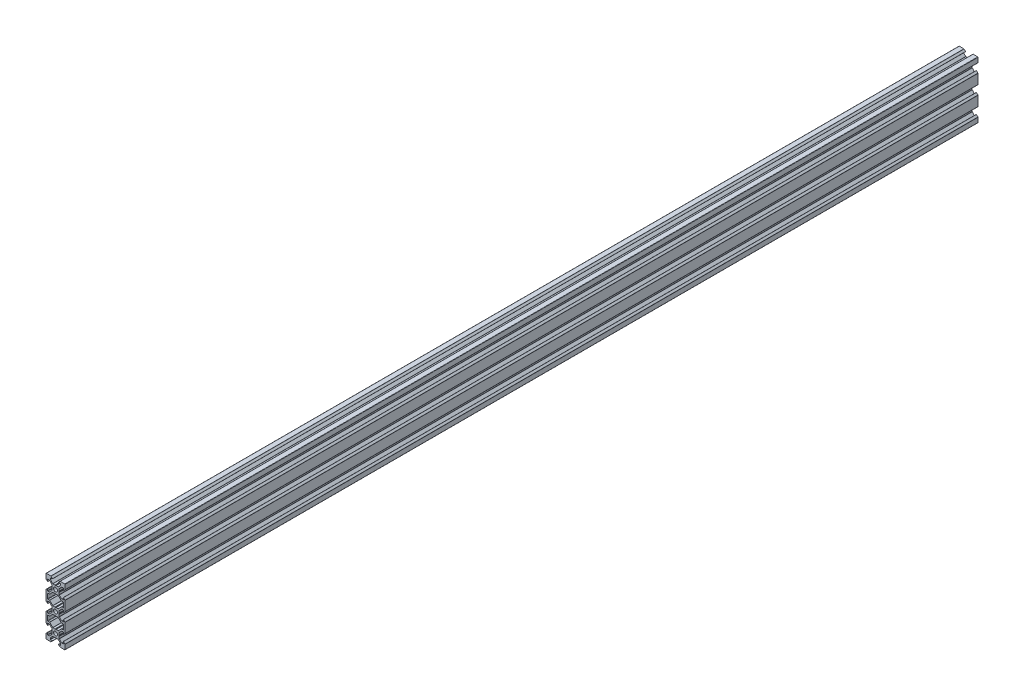
SolidWorks part; units mm, degrees
material "6063-T5"
ref_plane "Plan de face" through (0, 0, 0) normal (0, 0, 1) x (1, 0, 0)
ref_plane "Plan de dessus" through (0, 0, 0) normal (0, 1, 0) x (1, 0, 0)
ref_plane "Plan de droite" through (0, 0, 0) normal (1, 0, 0) x (0, 0, -1)
sketch "Esquisse1" plane through (0, 0, 0) normal (0, 0, 1) x (1, 0, 0)
  line L12 (10.4135, -7.6873) -> (8.8378, -7.6873)
  line L13 (8.6256, -7.5995) -> (5.4414, -4.4152)
  line L14 (5.2292, -4.3273) -> (3.0331, -4.3273)
  line L15 (3.0331, -4.3273) -> (2.5135, -4.0273)
  line L16 (2.5135, -4.0273) -> (1.9939, -4.3273)
  line L17 (1.9939, -4.3273) -> (-0.2022, -4.3273)
  line L18 (-0.4144, -4.4152) -> (-3.5986, -7.5995)
  line L19 (-3.8108, -7.6873) -> (-5.3865, -7.6873)
  line L20 (-5.6865, -7.9873) -> (-5.6865, -10.4267)
  line L21 (-5.6865, -10.4267) -> (-5.6865, -12.866)
  line L22 (-5.3865, -13.166) -> (-3.8108, -13.166)
  line L23 (-3.5986, -13.2539) -> (-0.4144, -16.4382)
  line L24 (-0.2022, -16.526) -> (1.9939, -16.526)
  line L25 (1.9939, -16.526) -> (2.5135, -16.826)
  line L26 (2.5135, -16.826) -> (3.0331, -16.526)
  line L27 (3.0331, -16.526) -> (5.2292, -16.526)
  line L28 (5.4414, -16.4382) -> (8.6256, -13.2539)
  line L29 (8.8378, -13.166) -> (10.4135, -13.166)
  line L30 (10.7135, -12.866) -> (10.7135, -10.4267)
  line L31 (10.7135, -10.4267) -> (10.7135, -7.9873)
  line L38 (10.4135, 12.3127) -> (8.8378, 12.3127)
  line L39 (8.6256, 12.4005) -> (5.4414, 15.5848)
  line L40 (5.2292, 15.6727) -> (3.0331, 15.6727)
  line L41 (3.0331, 15.6727) -> (2.5135, 15.9727)
  line L42 (2.5135, 15.9727) -> (1.9939, 15.6727)
  line L43 (1.9939, 15.6727) -> (-0.2022, 15.6727)
  line L44 (-0.4144, 15.5848) -> (-3.5986, 12.4005)
  line L45 (-3.8108, 12.3127) -> (-5.3865, 12.3127)
  line L46 (-5.6865, 12.0127) -> (-5.6865, 9.5733)
  line L47 (-5.6865, 9.5733) -> (-5.6865, 7.134)
  line L48 (-5.3865, 6.834) -> (-3.8108, 6.834)
  line L49 (-3.5986, 6.7461) -> (-0.4144, 3.5618)
  line L50 (-0.2022, 3.474) -> (1.9939, 3.474)
  line L51 (1.9939, 3.474) -> (2.5135, 3.174)
  line L52 (2.5135, 3.174) -> (3.0331, 3.474)
  line L53 (3.0331, 3.474) -> (5.2292, 3.474)
  line L54 (5.4414, 3.5618) -> (8.6256, 6.7461)
  line L55 (8.8378, 6.834) -> (10.4135, 6.834)
  line L56 (10.7135, 7.134) -> (10.7135, 9.5733)
  line L57 (10.7135, 9.5733) -> (10.7135, 12.0127)
  line L64 (6.1142, 19.5733) -> (6.4142, 20.0929)
  line L65 (6.4142, 20.0929) -> (6.4142, 22.2891)
  line L66 (6.502, 22.5012) -> (8.9856, 24.9848)
  line L67 (9.1978, 25.0727) -> (10.4135, 25.0727)
  line L68 (10.7135, 24.7727) -> (10.7135, 22.7733)
  line L69 (10.8842, 22.7026) -> (12.4256, 24.244)
  line L70 (12.5135, 24.4562) -> (12.5135, 29.2733)
  line L71 (12.2135, 29.5733) -> (7.3963, 29.5733)
  line L72 (7.1842, 29.4855) -> (5.6428, 27.944)
  line L73 (5.7135, 27.7733) -> (7.7128, 27.7733)
  line L74 (8.0128, 27.4733) -> (8.0128, 26.2576)
  line L75 (7.925, 26.0455) -> (5.4414, 23.5618)
  line L78 (5.2292, 23.474) -> (3.0331, 23.474)
  line L79 (3.0331, 23.474) -> (2.5135, 23.174)
  line L80 (2.5135, 23.174) -> (1.9939, 23.474)
  line L81 (1.9939, 23.474) -> (-0.2022, 23.474)
  line L84 (-0.4144, 23.5618) -> (-2.898, 26.0455)
  line L85 (-2.9858, 26.2576) -> (-2.9858, 27.4733)
  line L86 (-2.6858, 27.7733) -> (-0.6865, 27.7733)
  line L87 (-0.6158, 27.944) -> (-2.1572, 29.4855)
  line L88 (-2.3693, 29.5733) -> (-7.1865, 29.5733)
  line L89 (-7.4865, 29.2733) -> (-7.4865, 24.4562)
  line L90 (-7.3986, 24.244) -> (-5.8572, 22.7026)
  line L91 (-5.6865, 22.7733) -> (-5.6865, 24.7727)
  line L92 (-5.3865, 25.0727) -> (-4.1708, 25.0727)
  line L95 (-3.9586, 24.9848) -> (-1.475, 22.5012)
  line L96 (-1.3872, 22.2891) -> (-1.3872, 20.0929)
  line L97 (-1.3872, 20.0929) -> (-1.0872, 19.5733)
  line L98 (-1.0872, 19.5733) -> (-1.3872, 19.0537)
  line L99 (-1.3872, 19.0537) -> (-1.3872, 16.8576)
  line L100 (-1.475, 16.6455) -> (-3.9586, 14.1618)
  line L101 (-4.1708, 14.074) -> (-5.3865, 14.074)
  line L102 (-5.6865, 14.374) -> (-5.6865, 16.3733)
  line L103 (-5.8572, 16.444) -> (-7.3986, 14.9026)
  line L104 (-7.4865, 14.6905) -> (-7.4865, 9.5733)
  line L105 (-7.4865, 9.5733) -> (-7.4865, 4.4562)
  line L106 (-7.3986, 4.244) -> (-5.8572, 2.7026)
  line L107 (-5.6865, 2.7733) -> (-5.6865, 4.7727)
  line L108 (-5.3865, 5.0727) -> (-4.1708, 5.0727)
  line L109 (-3.9586, 4.9848) -> (-1.475, 2.5012)
  line L110 (-1.3872, 2.2891) -> (-1.3872, 0.0929)
  line L111 (-1.3872, 0.0929) -> (-1.0872, -0.4267)
  line L112 (-1.0872, -0.4267) -> (-1.3872, -0.9463)
  line L113 (-1.3872, -0.9463) -> (-1.3872, -3.1424)
  line L114 (-1.475, -3.3545) -> (-3.9586, -5.8382)
  line L115 (-4.1708, -5.926) -> (-5.3865, -5.926)
  line L116 (-5.6865, -5.626) -> (-5.6865, -3.6267)
  line L117 (-5.8572, -3.556) -> (-7.3986, -5.0974)
  line L118 (-7.4865, -5.3095) -> (-7.4865, -10.4267)
  line L119 (-7.4865, -10.4267) -> (-7.4865, -15.5438)
  line L120 (-7.3986, -15.756) -> (-5.8572, -17.2974)
  line L121 (-5.6865, -17.2267) -> (-5.6865, -15.2273)
  line L122 (-5.3865, -14.9273) -> (-4.1708, -14.9273)
  line L123 (-3.9586, -15.0152) -> (-1.475, -17.4988)
  line L124 (-1.3872, -17.7109) -> (-1.3872, -19.9071)
  line L125 (-1.3872, -19.9071) -> (-1.0872, -20.4267)
  line L126 (-1.0872, -20.4267) -> (-1.3872, -20.9463)
  line L127 (-1.3872, -20.9463) -> (-1.3872, -23.1424)
  line L128 (-1.475, -23.3545) -> (-3.9586, -25.8382)
  line L131 (-4.1708, -25.926) -> (-5.3865, -25.926)
  line L132 (-5.6865, -25.626) -> (-5.6865, -23.6267)
  line L133 (-5.8572, -23.556) -> (-7.3986, -25.0974)
  line L134 (-7.4865, -25.3095) -> (-7.4865, -30.1267)
  line L135 (-7.1865, -30.4267) -> (-2.3693, -30.4267)
  line L136 (-2.1572, -30.3388) -> (-0.6158, -28.7974)
  line L137 (-0.6865, -28.6267) -> (-2.6858, -28.6267)
  line L138 (-2.9858, -28.3267) -> (-2.9858, -27.1109)
  line L139 (-2.898, -26.8988) -> (-0.4144, -24.4152)
  line L142 (-0.2022, -24.3273) -> (1.9939, -24.3273)
  line L143 (1.9939, -24.3273) -> (2.5135, -24.0273)
  line L144 (2.5135, -24.0273) -> (3.0331, -24.3273)
  line L145 (3.0331, -24.3273) -> (5.2292, -24.3273)
  line L148 (5.4414, -24.4152) -> (7.925, -26.8988)
  line L149 (8.0128, -27.1109) -> (8.0128, -28.3267)
  line L150 (7.7128, -28.6267) -> (5.7135, -28.6267)
  line L151 (5.6428, -28.7974) -> (7.1842, -30.3388)
  line L152 (7.3963, -30.4267) -> (12.2135, -30.4267)
  line L153 (12.5135, -30.1267) -> (12.5135, -25.3095)
  line L154 (12.4256, -25.0974) -> (10.8842, -23.556)
  line L155 (10.7135, -23.6267) -> (10.7135, -25.626)
  line L156 (10.4135, -25.926) -> (9.1978, -25.926)
  line L157 (8.9856, -25.8382) -> (6.502, -23.3545)
  line L158 (6.4142, -23.1424) -> (6.4142, -20.9463)
  line L159 (6.4142, -20.9463) -> (6.1142, -20.4267)
  line L160 (6.1142, -20.4267) -> (6.4142, -19.9071)
  line L161 (6.4142, -19.9071) -> (6.4142, -17.7109)
  line L162 (6.502, -17.4988) -> (8.9856, -15.0152)
  line L163 (9.1978, -14.9273) -> (10.4135, -14.9273)
  line L164 (10.7135, -15.2273) -> (10.7135, -17.2267)
  line L165 (10.8842, -17.2974) -> (12.4256, -15.756)
  line L166 (12.5135, -15.5438) -> (12.5135, -10.4267)
  line L167 (12.5135, -10.4267) -> (12.5135, -5.3095)
  line L168 (12.4256, -5.0974) -> (10.8842, -3.556)
  line L169 (10.7135, -3.6267) -> (10.7135, -5.626)
  line L170 (10.4135, -5.926) -> (9.1978, -5.926)
  line L171 (8.9856, -5.8382) -> (6.502, -3.3545)
  line L172 (6.4142, -3.1424) -> (6.4142, -0.9463)
  line L173 (6.4142, -0.9463) -> (6.1142, -0.4267)
  line L174 (6.1142, -0.4267) -> (6.4142, 0.0929)
  line L175 (6.4142, 0.0929) -> (6.4142, 2.2891)
  line L176 (6.502, 2.5012) -> (8.9856, 4.9848)
  line L177 (9.1978, 5.0727) -> (10.4135, 5.0727)
  line L178 (10.7135, 4.7727) -> (10.7135, 2.7733)
  line L179 (10.8842, 2.7026) -> (12.4256, 4.244)
  line L180 (12.5135, 4.4562) -> (12.5135, 9.5733)
  line L181 (12.5135, 9.5733) -> (12.5135, 14.6905)
  line L182 (12.4256, 14.9026) -> (10.8842, 16.444)
  line L183 (10.7135, 16.3733) -> (10.7135, 14.374)
  line L184 (10.4135, 14.074) -> (9.1978, 14.074)
  line L185 (8.9856, 14.1618) -> (6.502, 16.6455)
  line L186 (6.4142, 16.8576) -> (6.4142, 19.0537)
  line L187 (6.4142, 19.0537) -> (6.1142, 19.5733)
  arc A0 (0.4135, -20.4267) -> (2.5135, -22.5267) centre (2.5135, -20.4267) ccw
  arc A1 (2.5135, -22.5267) -> (4.6135, -20.4267) centre (2.5135, -20.4267) ccw
  arc A2 (4.6135, -20.4267) -> (2.5135, -18.3267) centre (2.5135, -20.4267) ccw
  arc A3 (2.5135, -18.3267) -> (0.4135, -20.4267) centre (2.5135, -20.4267) ccw
  arc A4 (-0.2022, -24.3273) -> (-0.4144, -24.4152) centre (-0.2022, -24.6273) ccw
  arc A5 (5.4414, -24.4152) -> (5.2292, -24.3273) centre (5.2292, -24.6273) ccw
  arc A6 (-4.1708, -25.926) -> (-3.9586, -25.8382) centre (-4.1708, -25.626) ccw
  arc A7 (10.7135, -7.9873) -> (10.4135, -7.6873) centre (10.4135, -7.9873) ccw
  arc A8 (8.6256, -7.5995) -> (8.8378, -7.6873) centre (8.8378, -7.3873) ccw
  arc A9 (5.4414, -4.4152) -> (5.2292, -4.3273) centre (5.2292, -4.6273) ccw
  arc A10 (-0.2022, -4.3273) -> (-0.4144, -4.4152) centre (-0.2022, -4.6273) ccw
  arc A11 (-3.8108, -7.6873) -> (-3.5986, -7.5995) centre (-3.8108, -7.3873) ccw
  arc A12 (-5.3865, -7.6873) -> (-5.6865, -7.9873) centre (-5.3865, -7.9873) ccw
  arc A13 (-5.6865, -12.866) -> (-5.3865, -13.166) centre (-5.3865, -12.866) ccw
  arc A14 (-3.5986, -13.2539) -> (-3.8108, -13.166) centre (-3.8108, -13.466) ccw
  arc A15 (-0.4144, -16.4382) -> (-0.2022, -16.526) centre (-0.2022, -16.226) ccw
  arc A16 (5.2292, -16.526) -> (5.4414, -16.4382) centre (5.2292, -16.226) ccw
  arc A17 (8.8378, -13.166) -> (8.6256, -13.2539) centre (8.8378, -13.466) ccw
  arc A18 (10.4135, -13.166) -> (10.7135, -12.866) centre (10.4135, -12.866) ccw
  arc A19 (0.4135, -0.4267) -> (2.5135, -2.5267) centre (2.5135, -0.4267) ccw
  arc A20 (2.5135, -2.5267) -> (4.6135, -0.4267) centre (2.5135, -0.4267) ccw
  arc A21 (4.6135, -0.4267) -> (2.5135, 1.6733) centre (2.5135, -0.4267) ccw
  arc A22 (2.5135, 1.6733) -> (0.4135, -0.4267) centre (2.5135, -0.4267) ccw
  arc A23 (10.7135, 12.0127) -> (10.4135, 12.3127) centre (10.4135, 12.0127) ccw
  arc A24 (8.6256, 12.4005) -> (8.8378, 12.3127) centre (8.8378, 12.6127) ccw
  arc A25 (5.4414, 15.5848) -> (5.2292, 15.6727) centre (5.2292, 15.3727) ccw
  arc A26 (-0.2022, 15.6727) -> (-0.4144, 15.5848) centre (-0.2022, 15.3727) ccw
  arc A27 (-3.8108, 12.3127) -> (-3.5986, 12.4005) centre (-3.8108, 12.6127) ccw
  arc A28 (-5.3865, 12.3127) -> (-5.6865, 12.0127) centre (-5.3865, 12.0127) ccw
  arc A29 (-5.6865, 7.134) -> (-5.3865, 6.834) centre (-5.3865, 7.134) ccw
  arc A30 (-3.5986, 6.7461) -> (-3.8108, 6.834) centre (-3.8108, 6.534) ccw
  arc A31 (-0.4144, 3.5618) -> (-0.2022, 3.474) centre (-0.2022, 3.774) ccw
  arc A32 (5.2292, 3.474) -> (5.4414, 3.5618) centre (5.2292, 3.774) ccw
  arc A33 (8.8378, 6.834) -> (8.6256, 6.7461) centre (8.8378, 6.534) ccw
  arc A34 (10.4135, 6.834) -> (10.7135, 7.134) centre (10.4135, 7.134) ccw
  arc A35 (-0.4144, 23.5618) -> (-0.2022, 23.474) centre (-0.2022, 23.774) ccw
  arc A36 (5.2292, 23.474) -> (5.4414, 23.5618) centre (5.2292, 23.774) ccw
  arc A37 (-3.9586, 24.9848) -> (-4.1708, 25.0727) centre (-4.1708, 24.7727) ccw
  arc A38 (0.4135, 19.5733) -> (2.5135, 17.4733) centre (2.5135, 19.5733) ccw
  arc A39 (2.5135, 17.4733) -> (4.6135, 19.5733) centre (2.5135, 19.5733) ccw
  arc A40 (4.6135, 19.5733) -> (2.5135, 21.6733) centre (2.5135, 19.5733) ccw
  arc A41 (2.5135, 21.6733) -> (0.4135, 19.5733) centre (2.5135, 19.5733) ccw
  arc A42 (6.502, 22.5012) -> (6.4142, 22.2891) centre (6.7142, 22.2891) ccw
  arc A43 (9.1978, 25.0727) -> (8.9856, 24.9848) centre (9.1978, 24.7727) ccw
  arc A44 (10.7135, 24.7727) -> (10.4135, 25.0727) centre (10.4135, 24.7727) ccw
  arc A45 (10.7135, 22.7733) -> (10.8842, 22.7026) centre (10.8135, 22.7733) ccw
  arc A46 (12.4256, 24.244) -> (12.5135, 24.4562) centre (12.2135, 24.4562) ccw
  arc A47 (12.5135, 29.2733) -> (12.2135, 29.5733) centre (12.2135, 29.2733) ccw
  arc A48 (7.3963, 29.5733) -> (7.1842, 29.4855) centre (7.3963, 29.2733) ccw
  arc A49 (5.6428, 27.944) -> (5.7135, 27.7733) centre (5.7135, 27.8733) ccw
  arc A50 (8.0128, 27.4733) -> (7.7128, 27.7733) centre (7.7128, 27.4733) ccw
  arc A51 (7.925, 26.0455) -> (8.0128, 26.2576) centre (7.7128, 26.2576) ccw
  arc A52 (-2.9858, 26.2576) -> (-2.898, 26.0455) centre (-2.6858, 26.2576) ccw
  arc A53 (-2.6858, 27.7733) -> (-2.9858, 27.4733) centre (-2.6858, 27.4733) ccw
  arc A54 (-0.6865, 27.7733) -> (-0.6158, 27.944) centre (-0.6865, 27.8733) ccw
  arc A55 (-2.1572, 29.4855) -> (-2.3693, 29.5733) centre (-2.3693, 29.2733) ccw
  arc A56 (-7.1865, 29.5733) -> (-7.4865, 29.2733) centre (-7.1865, 29.2733) ccw
  arc A57 (-7.4865, 24.4562) -> (-7.3986, 24.244) centre (-7.1865, 24.4562) ccw
  arc A58 (-5.8572, 22.7026) -> (-5.6865, 22.7733) centre (-5.7865, 22.7733) ccw
  arc A59 (-5.3865, 25.0727) -> (-5.6865, 24.7727) centre (-5.3865, 24.7727) ccw
  arc A60 (-1.3872, 22.2891) -> (-1.475, 22.5012) centre (-1.6872, 22.2891) ccw
  arc A61 (-1.475, 16.6455) -> (-1.3872, 16.8576) centre (-1.6872, 16.8576) ccw
  arc A62 (-4.1708, 14.074) -> (-3.9586, 14.1618) centre (-4.1708, 14.374) ccw
  arc A63 (-5.6865, 14.374) -> (-5.3865, 14.074) centre (-5.3865, 14.374) ccw
  arc A64 (-5.6865, 16.3733) -> (-5.8572, 16.444) centre (-5.7865, 16.3733) ccw
  arc A65 (-7.3986, 14.9026) -> (-7.4865, 14.6905) centre (-7.1865, 14.6905) ccw
  arc A66 (-7.4865, 4.4562) -> (-7.3986, 4.244) centre (-7.1865, 4.4562) ccw
  arc A67 (-5.8572, 2.7026) -> (-5.6865, 2.7733) centre (-5.7865, 2.7733) ccw
  arc A68 (-5.3865, 5.0727) -> (-5.6865, 4.7727) centre (-5.3865, 4.7727) ccw
  arc A69 (-3.9586, 4.9848) -> (-4.1708, 5.0727) centre (-4.1708, 4.7727) ccw
  arc A70 (-1.3872, 2.2891) -> (-1.475, 2.5012) centre (-1.6872, 2.2891) ccw
  arc A71 (-1.475, -3.3545) -> (-1.3872, -3.1424) centre (-1.6872, -3.1424) ccw
  arc A72 (-4.1708, -5.926) -> (-3.9586, -5.8382) centre (-4.1708, -5.626) ccw
  arc A73 (-5.6865, -5.626) -> (-5.3865, -5.926) centre (-5.3865, -5.626) ccw
  arc A74 (-5.6865, -3.6267) -> (-5.8572, -3.556) centre (-5.7865, -3.6267) ccw
  arc A75 (-7.3986, -5.0974) -> (-7.4865, -5.3095) centre (-7.1865, -5.3095) ccw
  arc A76 (-7.4865, -15.5438) -> (-7.3986, -15.756) centre (-7.1865, -15.5438) ccw
  arc A77 (-5.8572, -17.2974) -> (-5.6865, -17.2267) centre (-5.7865, -17.2267) ccw
  arc A78 (-5.3865, -14.9273) -> (-5.6865, -15.2273) centre (-5.3865, -15.2273) ccw
  arc A79 (-3.9586, -15.0152) -> (-4.1708, -14.9273) centre (-4.1708, -15.2273) ccw
  arc A80 (-1.3872, -17.7109) -> (-1.475, -17.4988) centre (-1.6872, -17.7109) ccw
  arc A81 (-1.475, -23.3545) -> (-1.3872, -23.1424) centre (-1.6872, -23.1424) ccw
  arc A82 (-5.6865, -25.626) -> (-5.3865, -25.926) centre (-5.3865, -25.626) ccw
  arc A83 (-5.6865, -23.6267) -> (-5.8572, -23.556) centre (-5.7865, -23.6267) ccw
  arc A84 (-7.3986, -25.0974) -> (-7.4865, -25.3095) centre (-7.1865, -25.3095) ccw
  arc A85 (-7.4865, -30.1267) -> (-7.1865, -30.4267) centre (-7.1865, -30.1267) ccw
  arc A86 (-2.3693, -30.4267) -> (-2.1572, -30.3388) centre (-2.3693, -30.1267) ccw
  arc A87 (-0.6158, -28.7974) -> (-0.6865, -28.6267) centre (-0.6865, -28.7267) ccw
  arc A88 (-2.9858, -28.3267) -> (-2.6858, -28.6267) centre (-2.6858, -28.3267) ccw
  arc A89 (-2.898, -26.8988) -> (-2.9858, -27.1109) centre (-2.6858, -27.1109) ccw
  arc A90 (8.0128, -27.1109) -> (7.925, -26.8988) centre (7.7128, -27.1109) ccw
  arc A91 (7.7128, -28.6267) -> (8.0128, -28.3267) centre (7.7128, -28.3267) ccw
  arc A92 (5.7135, -28.6267) -> (5.6428, -28.7974) centre (5.7135, -28.7267) ccw
  arc A93 (7.1842, -30.3388) -> (7.3963, -30.4267) centre (7.3963, -30.1267) ccw
  arc A94 (12.2135, -30.4267) -> (12.5135, -30.1267) centre (12.2135, -30.1267) ccw
  arc A95 (12.5135, -25.3095) -> (12.4256, -25.0974) centre (12.2135, -25.3095) ccw
  arc A96 (10.8842, -23.556) -> (10.7135, -23.6267) centre (10.8135, -23.6267) ccw
  arc A97 (10.4135, -25.926) -> (10.7135, -25.626) centre (10.4135, -25.626) ccw
  arc A98 (8.9856, -25.8382) -> (9.1978, -25.926) centre (9.1978, -25.626) ccw
  arc A99 (6.4142, -23.1424) -> (6.502, -23.3545) centre (6.7142, -23.1424) ccw
  arc A100 (6.502, -17.4988) -> (6.4142, -17.7109) centre (6.7142, -17.7109) ccw
  arc A101 (9.1978, -14.9273) -> (8.9856, -15.0152) centre (9.1978, -15.2273) ccw
  arc A102 (10.7135, -15.2273) -> (10.4135, -14.9273) centre (10.4135, -15.2273) ccw
  arc A103 (10.7135, -17.2267) -> (10.8842, -17.2974) centre (10.8135, -17.2267) ccw
  arc A104 (12.4256, -15.756) -> (12.5135, -15.5438) centre (12.2135, -15.5438) ccw
  arc A105 (12.5135, -5.3095) -> (12.4256, -5.0974) centre (12.2135, -5.3095) ccw
  arc A106 (10.8842, -3.556) -> (10.7135, -3.6267) centre (10.8135, -3.6267) ccw
  arc A107 (10.4135, -5.926) -> (10.7135, -5.626) centre (10.4135, -5.626) ccw
  arc A108 (8.9856, -5.8382) -> (9.1978, -5.926) centre (9.1978, -5.626) ccw
  arc A109 (6.4142, -3.1424) -> (6.502, -3.3545) centre (6.7142, -3.1424) ccw
  arc A110 (6.502, 2.5012) -> (6.4142, 2.2891) centre (6.7142, 2.2891) ccw
  arc A111 (9.1978, 5.0727) -> (8.9856, 4.9848) centre (9.1978, 4.7727) ccw
  arc A112 (10.7135, 4.7727) -> (10.4135, 5.0727) centre (10.4135, 4.7727) ccw
  arc A113 (10.7135, 2.7733) -> (10.8842, 2.7026) centre (10.8135, 2.7733) ccw
  arc A114 (12.4256, 4.244) -> (12.5135, 4.4562) centre (12.2135, 4.4562) ccw
  arc A115 (12.5135, 14.6905) -> (12.4256, 14.9026) centre (12.2135, 14.6905) ccw
  arc A116 (10.8842, 16.444) -> (10.7135, 16.3733) centre (10.8135, 16.3733) ccw
  arc A117 (10.4135, 14.074) -> (10.7135, 14.374) centre (10.4135, 14.374) ccw
  arc A118 (8.9856, 14.1618) -> (9.1978, 14.074) centre (9.1978, 14.374) ccw
  arc A119 (6.4142, 16.8576) -> (6.502, 16.6455) centre (6.7142, 16.8576) ccw
  dimension "D1" = 60
extrude "Boss.-Extru.1" add sketch "Esquisse1" along normal blind 960
